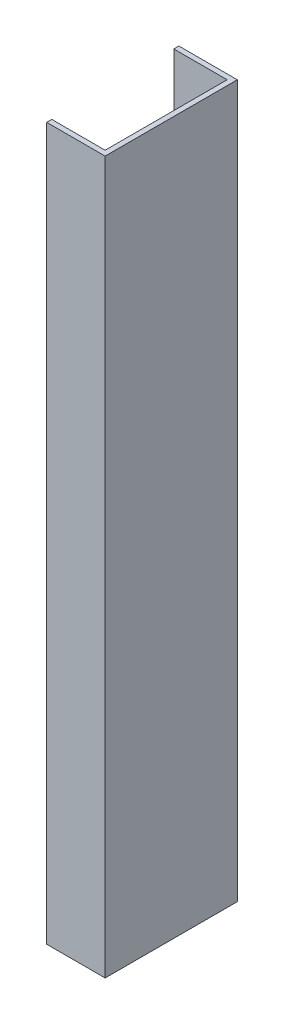
SolidWorks part; units mm, degrees
ref_plane "Alzado" through (0, 0, 0) normal (0, 0, 1) x (1, 0, 0)
ref_plane "Planta" through (0, 0, 0) normal (0, 1, 0) x (1, 0, 0)
ref_plane "Vista lateral" through (0, 0, 0) normal (1, 0, 0) x (0, 0, -1)
sketch "Croquis1" plane through (0, 0, 0) normal (0, 1, 0) x (1, 0, 0)
  line L0 (0, 41.275) -> (0, -41.275)
  line L1 (0, 41.275) -> (-36.5125, 41.275)
  line L2 (0, -41.275) -> (-36.5125, -41.275)
  line L3 (-36.5125, -41.275) -> (-36.5125, -38.1)
  line L4 (-36.5125, -38.1) -> (-3.175, -38.1)
  line L5 (-3.175, -38.1) -> (-3.175, 38.1)
  line L6 (-3.175, 38.1) -> (-36.5125, 38.1)
  line L7 (-36.5125, 38.1) -> (-36.5125, 41.275)
  point P4 (0, 0)
  dimension "D1" = 3.175
  dimension "D2" = 3.175
  dimension "D3" = 3.175
  dimension "D4" = 76.2
  dimension "D5" = 33.3375
  dimension "D6" = 33.3375
extrude "Saliente-Extruir1" add sketch "Croquis1" along normal mid plane 444.5
